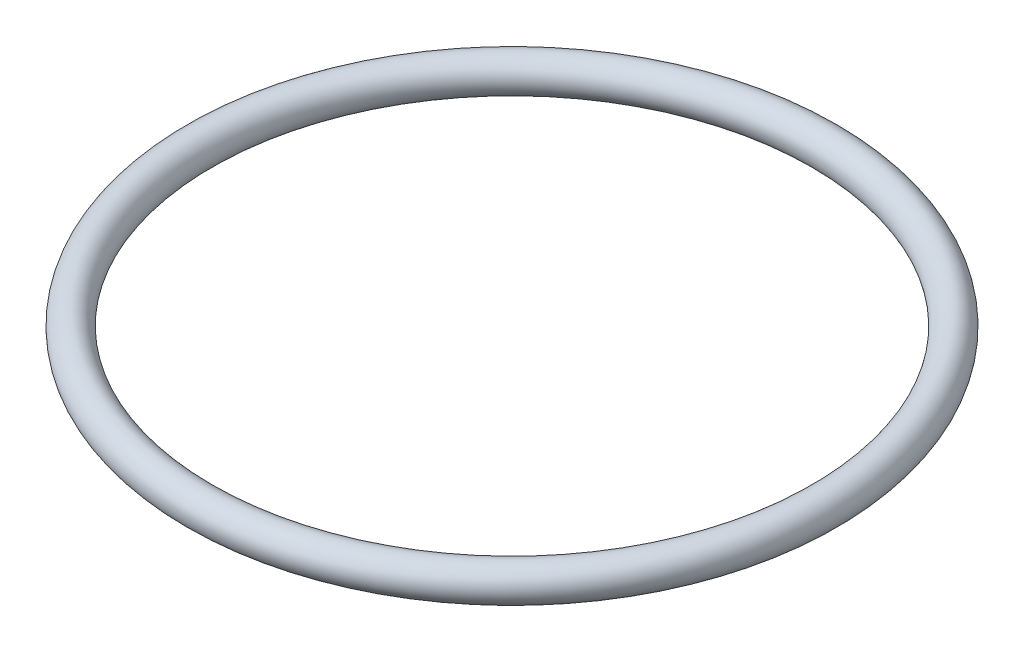
SolidWorks part; units mm, degrees
material "NBR"
ref_plane "前视基准面" through (0, 0, 0) normal (0, 0, 1) x (1, 0, 0)
ref_plane "上视基准面" through (0, 0, 0) normal (0, 1, 0) x (1, 0, 0)
ref_plane "右视基准面" through (0, 0, 0) normal (1, 0, 0) x (0, 0, -1)
ref_axis "基准轴1" through (0, 55, 0) along (0, -1, 0)
sketch "草图1" plane through (0, 0, 0) normal (0, 0, 1) x (1, 0, 0)
  line L0 (0, 55) -> (0, -55) construction
  circle A0 centre (31.775, 1.6787) radius 1.775
  dimension "D1" = 3.55
  dimension "D2" = 31.775
revolve "旋转1" add sketch "草图1" angle 360 about axis through (0, 55, 0) along (0, -1, 0)
